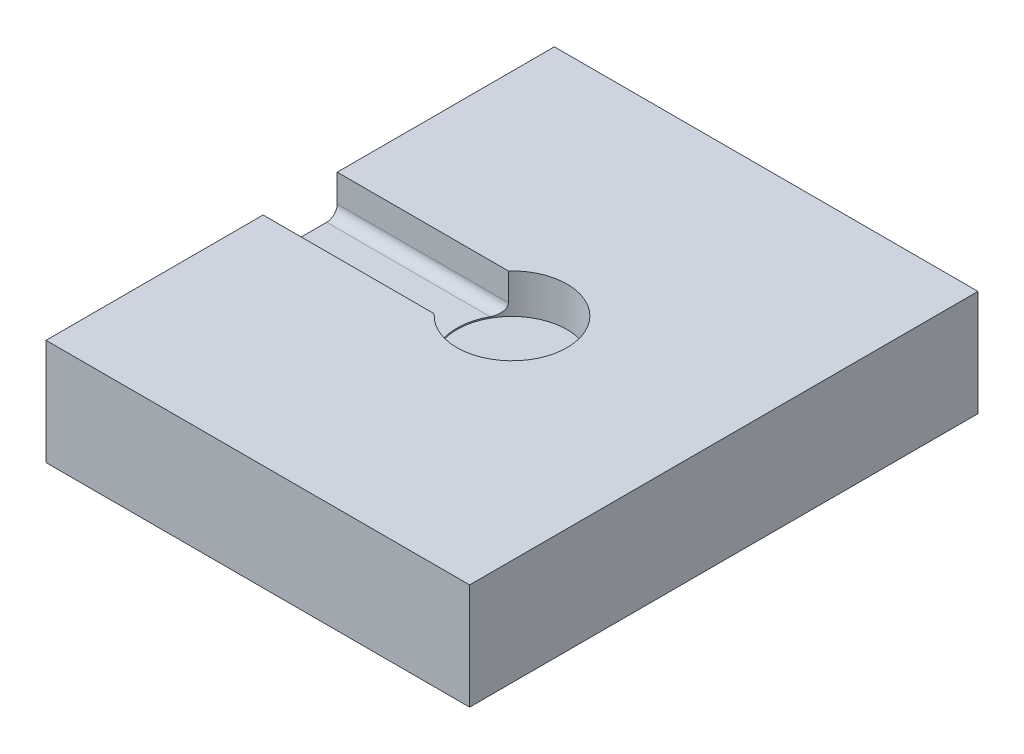
SolidWorks part; units mm, degrees
ref_plane "Front Plane" through (0, 0, 0) normal (0, 0, 1) x (1, 0, 0)
ref_plane "Top Plane" through (0, 0, 0) normal (0, 1, 0) x (1, 0, 0)
ref_plane "Right Plane" through (0, 0, 0) normal (1, 0, 0) x (0, 0, -1)
sketch "Sketch1" plane through (0, 0, 0) normal (0, 1, 0) x (1, 0, 0)
  line L1 (100, 120) -> (-100, 120)
  line L2 (100, 120) -> (100, -120)
  line L3 (100, -120) -> (-100, -120)
  line L4 (-100, 120) -> (-100, -120)
  line L5 (100, 120) -> (-100, -120) construction
  line L6 (100, -120) -> (-100, 120) construction
  point P0 (0, 0)
  dimension "D1" = 240
  dimension "D2" = 200
extrude "base" add sketch "Sketch1" along normal blind 50
sketch "Sketch2" plane through (0, 50, 0) normal (0, 1, 0) x (1, 0, 0)
  circle A0 centre (0, 0) radius 26
  dimension "D1" = 52
extrude "load cell cut" cut sketch "Sketch2" against normal blind 18.6 contours A0
sketch "Sketch3" plane through (-100, 0, 0) normal (1, 0, 0) x (0, 0, -1)
  line L1 (-17.5, 32) -> (17.5, 32)
  line L2 (-17.5, 32) -> (-17.5, 50)
  line L3 (-17.5, 50) -> (17.5, 50)
  line L4 (17.5, 32) -> (17.5, 50)
  line L5 (-120, 50) -> (120, 50) construction
  line L6 (-120, 0) -> (120, 0) construction
  point P6 (0, 32)
  point P10 (0, 0)
  dimension "D1" = 18
  dimension "D2" = 35
extrude "wire cut" cut sketch "Sketch3" along normal up to next
fillet "wire cut fillet" radius 5 2 edges at (-59.6144, 32, 17.5) (-59.6144, 32, -17.5)
